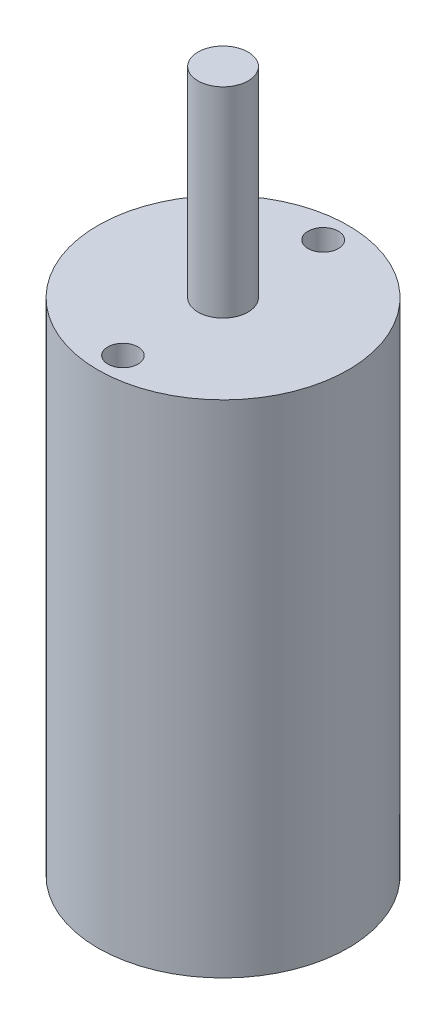
SolidWorks part; units mm, degrees
ref_plane "前视基准面" through (0, 0, 0) normal (0, 0, 1) x (1, 0, 0)
ref_plane "上视基准面" through (0, 0, 0) normal (0, 1, 0) x (1, 0, 0)
ref_plane "右视基准面" through (0, 0, 0) normal (1, 0, 0) x (0, 0, -1)
sketch "草图1" plane through (0, 0, 0) normal (0, 1, 0) x (1, 0, 0)
  circle A0 centre (0, 0) radius 12.5
  dimension "D1" = 25
extrude "凸台-拉伸1" add sketch "草图1" along normal blind 50
sketch "草图2" plane through (0, 50, 0) normal (0, 1, 0) x (1, 0, 0)
  circle A0 centre (0, -10) radius 1.5
  circle A1 centre (0, 10) radius 1.5124
extrude "切除-拉伸1" cut sketch "草图2" against normal blind 10
sketch "草图3" plane through (0, 50, 0) normal (0, 1, 0) x (1, 0, 0)
  circle A0 centre (0, 0) radius 2.5
  dimension "D1" = 5
extrude "凸台-拉伸2" add sketch "草图3" along normal blind 20
